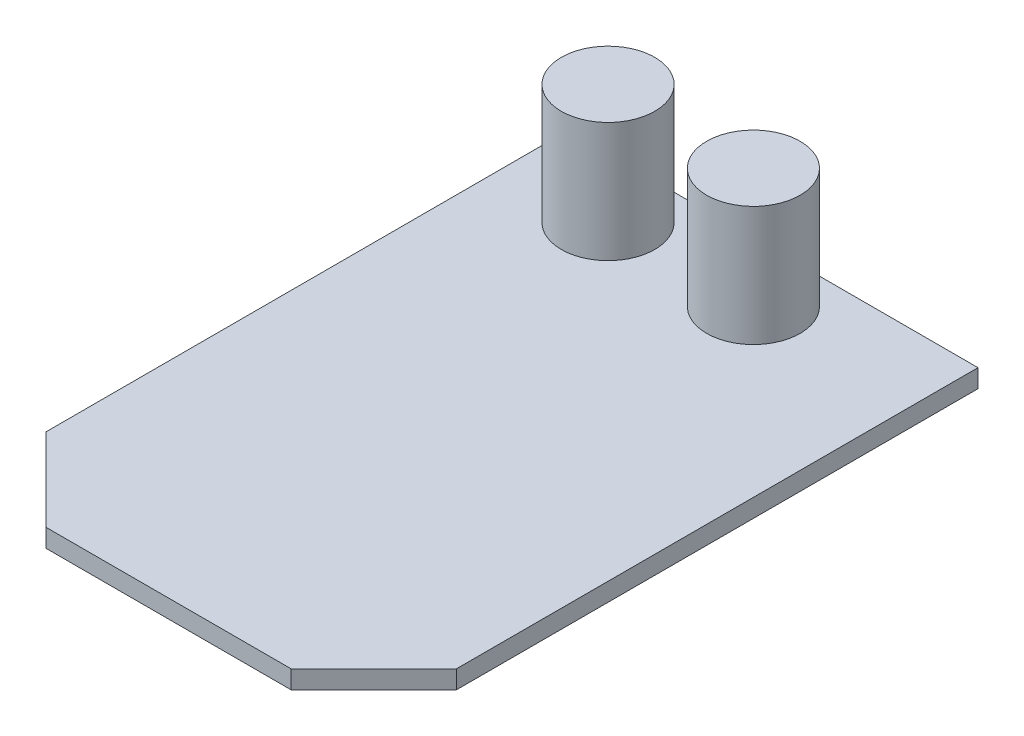
SolidWorks part; units mm, degrees
ref_plane "Front Plane" through (0, 0, 0) normal (0, 0, 1) x (1, 0, 0)
ref_plane "Top Plane" through (0, 0, 0) normal (0, 1, 0) x (1, 0, 0)
ref_plane "Right Plane" through (0, 0, 0) normal (1, 0, 0) x (0, 0, -1)
sketch "Sketch1" plane through (0, 0, 0) normal (0, 1, 0) x (1, 0, 0)
  line L0 (-18, -19.25) -> (-10.75, -26.5)
  line L1 (-18, -26.5) -> (18, -26.5)
  line L2 (-18, -26.5) -> (-18, 26.5)
  line L3 (-18, 26.5) -> (18, 26.5)
  line L4 (18, -26.5) -> (18, 26.5)
  line L5 (-18, -26.5) -> (18, 26.5) construction
  line L6 (-18, 26.5) -> (18, -26.5) construction
  line L7 (18, -19.25) -> (10.75, -26.5)
  point P0 (0, 0)
  dimension "D1" = 36
  dimension "D2" = 53
  dimension "D3" = 7.25
  dimension "D4" = 7.25
  dimension "D5" = 7.25
extrude "Boss-Extrude1" add sketch "Sketch1" along normal blind 1.6 contours L7 L4 L3 L2 L0 L1
sketch "Sketch2" plane through (0, 0, 0) normal (0, -1, 0) x (1, 0, 0)
  line L0 (-18, -26.5) -> (18, -26.5) construction
  line L1 (15, -12.2) -> (-15, -12.2)
  line L2 (15, -12.2) -> (15, -17.2)
  line L3 (15, -17.2) -> (-15, -17.2)
  line L4 (-15, -12.2) -> (-15, -17.2)
  line L5 (15, -12.2) -> (-15, -17.2) construction
  line L6 (15, -17.2) -> (-15, -12.2) construction
  point P0 (0, -14.7)
  dimension "D1" = 5
  dimension "D2" = 30
  dimension "D3" = 9.3
extrude "Boss-Extrude2" add sketch "Sketch2" along normal blind 1.15
sketch "Sketch3" plane through (0, 1.6, 0) normal (0, 1, 0) x (1, 0, 0)
  line L0 (-18, -19.25) -> (-18, 26.5) construction
  line L1 (-18, 26.5) -> (18, 26.5) construction
  circle A0 centre (-9.25, 21.3) radius 4.1
  circle A1 centre (3.5, 21.3) radius 4.1
  dimension "D1" = 8.2
  dimension "D2" = 8.2
  dimension "D3" = 8.75
  dimension "D4" = 21.5
  dimension "D5" = 5.2
  dimension "D6" = 5.2
extrude "Boss-Extrude3" add sketch "Sketch3" along normal blind 10.5
